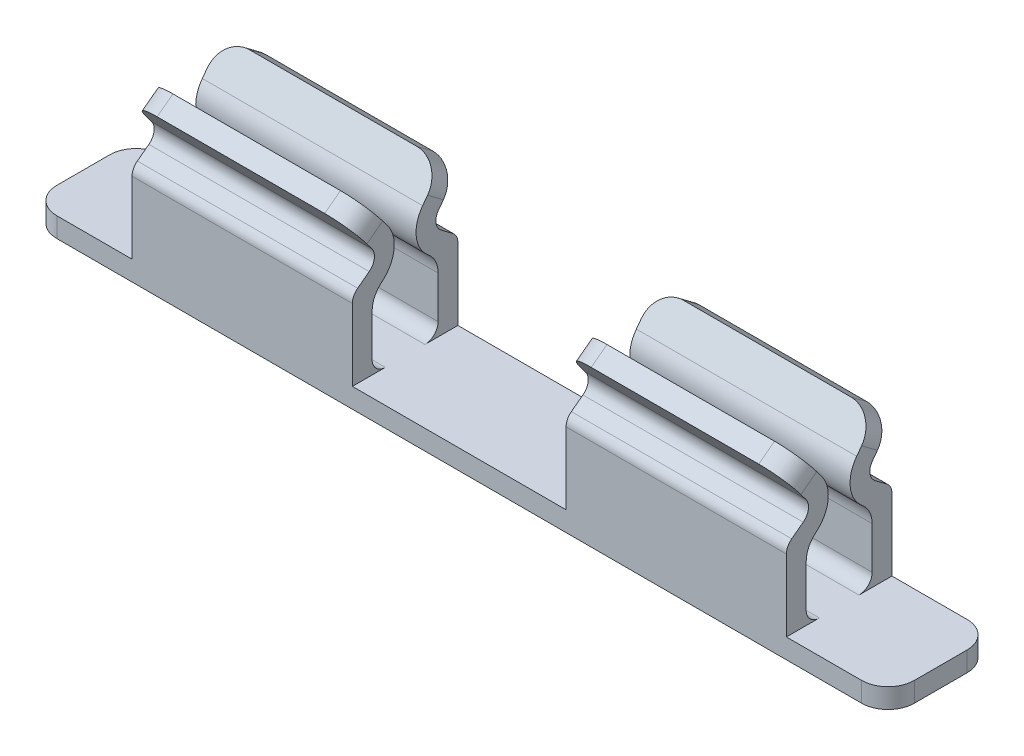
SolidWorks part; units mm, degrees
ref_plane "Спереди" through (0, 0, 0) normal (0, 0, 1) x (1, 0, 0)
ref_plane "Сверху" through (0, 0, 0) normal (0, 1, 0) x (1, 0, 0)
ref_plane "Справа" through (0, 0, 0) normal (1, 0, 0) x (0, 0, -1)
sketch "Эскиз1" plane through (0, 0, 0) normal (1, 0, 0) x (0, 0, -1)
  line L0 (-0.4, 0) -> (0.4, 0)
  line L1 (-0.4, 0) -> (-0.4, 0.6944)
  line L2 (-0.36, 0.7744) -> (-0.2725, 0.84)
  line L3 (-0.2525, 0.98) -> (-0.41, 1.19)
  line L4 (-0.41, 1.19) -> (-0.29, 1.28)
  line L5 (-0.29, 1.28) -> (-0.1325, 1.07)
  line L6 (-0.1825, 0.72) -> (-0.17, 0.7294)
  line L7 (-0.25, 0.5694) -> (-0.25, 0.25)
  line L8 (-0.15, 0.15) -> (0.15, 0.15)
  line L9 (0, 0) -> (0, 1.3794) construction
  line L10 (0.25, 0.5694) -> (0.25, 0.25)
  line L11 (0.4, 0) -> (0.4, 0.6944)
  line L12 (0.36, 0.7744) -> (0.2725, 0.84)
  line L13 (0.1825, 0.72) -> (0.17, 0.7294)
  line L14 (0.2525, 0.98) -> (0.41, 1.19)
  line L15 (0.41, 1.19) -> (0.29, 1.28)
  line L16 (0.29, 1.28) -> (0.1325, 1.07)
  arc A0 (-0.1325, 1.07) -> (-0.1825, 0.72) centre (-0.3325, 0.92) cw
  arc A1 (-0.17, 0.7294) -> (-0.25, 0.5694) centre (-0.05, 0.5694) ccw
  arc A2 (-0.25, 0.25) -> (-0.15, 0.15) centre (-0.15, 0.25) ccw
  arc A3 (-0.4, 0.6944) -> (-0.36, 0.7744) centre (-0.3, 0.6944) cw
  arc A4 (-0.2725, 0.84) -> (-0.2525, 0.98) centre (-0.3325, 0.92) ccw
  arc A5 (0.25, 0.25) -> (0.15, 0.15) centre (0.15, 0.25) cw
  arc A6 (0.4, 0.6944) -> (0.36, 0.7744) centre (0.3, 0.6944) ccw
  arc A7 (0.17, 0.7294) -> (0.25, 0.5694) centre (0.05, 0.5694) cw
  arc A8 (0.1325, 1.07) -> (0.1825, 0.72) centre (0.3325, 0.92) ccw
  arc A9 (0.2725, 0.84) -> (0.2525, 0.98) centre (0.3325, 0.92) cw
  point P1 (0, 0)
  point P2 (0, 0)
  point P3 (-0.0945, 0.807)
  point P4 (0, 0)
  point P15 (-0.0575, 0.8497)
  point P16 (0, 0)
  point P17 (-0.1925, 0.8844)
  point P28 (-0.1925, 0.9)
  point P30 (0, 0.15)
  point P48 (0.4, 0)
  point P51 (-0.4, 0)
  dimension "D10" = 0.25
  dimension "D11" = 0.2
  dimension "D12" = 0.1
  dimension "D13" = 0.1
  dimension "D1" = 0.8
  dimension "D2" = 1.28
  dimension "D3" = 0.82
  dimension "D4" = 0.58
  dimension "D5" = 0.9
  dimension "D6" = 0.15
  dimension "D7" = 0.15
  dimension "D8" = 0.15
  dimension "D9" = 0.15
extrude "Бобышка-Вытянуть1" add sketch "Эскиз1" along normal mid plane 6.5
sketch "Эскиз2" plane through (0, 0, 0) normal (0, 0, 1) x (1, 0, 0)
  line L0 (0, 0) -> (0, 2.0101) construction
  line L1 (-1.645, 1.28) -> (-1.645, 0) construction
  line L2 (3.25, 1.28) -> (-3.25, 1.28) construction
  line L3 (-2.48, 1.28) -> (-0.81, 1.28) construction
  line L5 (-0.81, 1.28) -> (0.81, 1.28)
  line L6 (-0.81, 1.28) -> (-0.81, 0.15)
  line L7 (-0.81, 0.15) -> (0.81, 0.15)
  line L8 (0.81, 1.28) -> (0.81, 0.15)
  line L9 (-3.25, 0.6944) -> (-3.25, 0) construction
  line L10 (-2.48, 1.28) -> (-3.25, 1.28)
  line L11 (-2.48, 1.28) -> (-2.48, 0.15)
  line L12 (-2.48, 0.15) -> (-3.25, 0.15)
  line L13 (-3.25, 1.28) -> (-3.25, 0.15)
  line L14 (3.25, 0) -> (-3.25, 0) construction
  line L15 (3.25, 1.28) -> (2.48, 1.28)
  line L16 (3.25, 1.28) -> (3.25, 0.15)
  line L17 (3.25, 0.15) -> (2.48, 0.15)
  line L18 (2.48, 1.28) -> (2.48, 0.15)
  point P9 (-1.645, 1.28)
  point P25 (0, 0)
  dimension "D1" = 1.645
  dimension "D2" = 1.67
  dimension "D3" = 0.15
extrude "Вырез-Вытянуть1" cut sketch "Эскиз2" against normal through all both and the other way through all
fillet "Скругление1" radius 0.2 12 edges at (3.25, 0.075, -0.4) (3.25, 0.075, 0.4) (2.48, 1.235, 0.35) (2.48, 1.235, -0.35) (0.81, 1.235, -0.35) (0.81, 1.235, 0.35) (-0.81, 1.235, -0.35) (-0.81, 1.235, 0.35) (-2.48, 1.235, -0.35) (-2.48, 1.235, 0.35) (-3.25, 0.075, -0.4) (-3.25, 0.075, 0.4)
